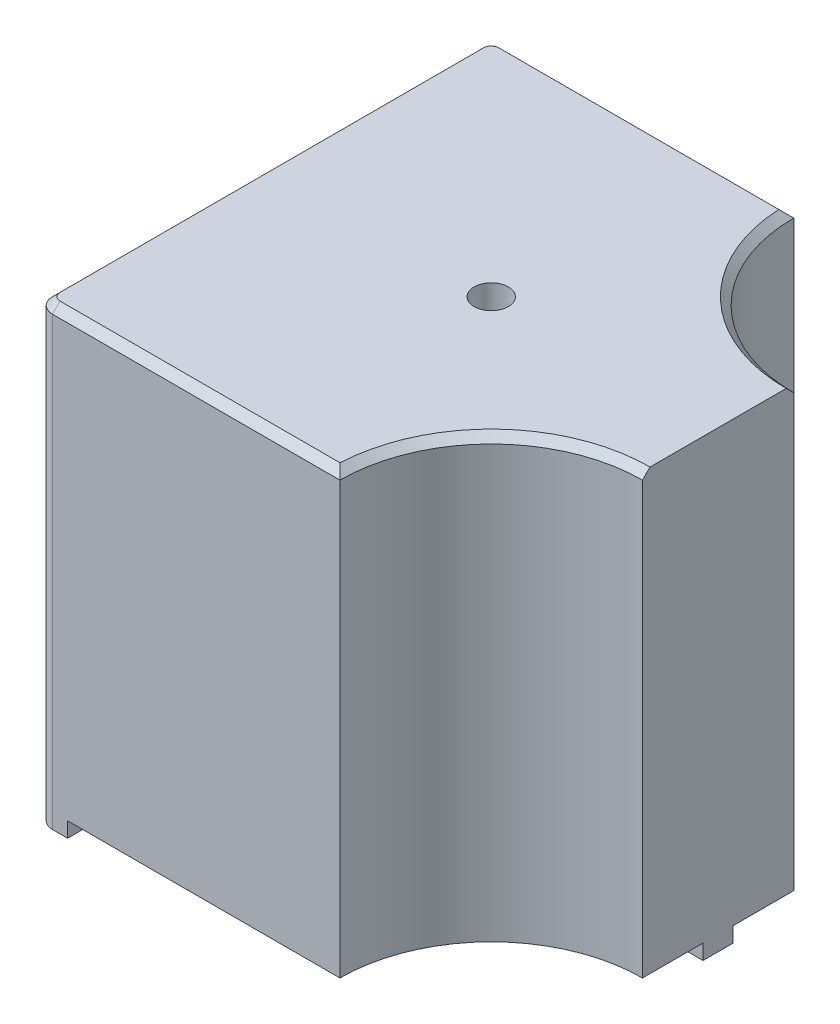
SolidWorks part; units mm, degrees
material "Copper"
ref_plane "Front" through (0, 0, 0) normal (0, 0, 1) x (1, 0, 0)
ref_plane "Top" through (0, 0, 0) normal (0, 1, 0) x (1, 0, 0)
ref_plane "Right" through (0, 0, 0) normal (1, 0, 0) x (0, 0, -1)
sketch "Sketch1" plane through (0, 0, 0) normal (0, 1, 0) x (1, 0, 0)
  line L1 (-15, 15) -> (15, 15)
  line L2 (-15, 15) -> (-15, -15)
  line L3 (-15, -15) -> (15, -15)
  line L4 (15, 15) -> (15, -15)
  line L5 (-15, 15) -> (15, -15) construction
  line L6 (-15, -15) -> (15, 15) construction
  point P0 (0, 0)
  dimension "D1" = 30
  dimension "D2" = 30
extrude "Boss-Extrude1" add sketch "Sketch1" along normal blind 30
sketch "Sketch2" plane through (0, 30, 0) normal (0, 1, 0) x (1, 0, 0)
  line L0 (15, -15) -> (15, 15) construction
  line L1 (15, 15) -> (-15, 15) construction
  arc A0 (15, 5) -> (5, 15) centre (15, 15) cw
extrude "Cut-Extrude1" cut sketch "Sketch2" against normal through all and the other way through all flip side to cut
mirror "Mirror1" about plane through (0, 0, 0) normal (0, 0, 1) of "Cut-Extrude1"
sketch "Sketch3" plane through (0, 0, 0) normal (0, -1, 0) x (1, 0, 0)
  line L0 (15, 5) -> (15, -5) construction
  line L1 (-15, 15) -> (-13, 15)
  line L2 (-15, 15) -> (-15, 13)
  line L3 (-15, 13) -> (-13, 13)
  line L4 (-13, 15) -> (-13, 13)
  line L5 (-15, -15) -> (-13, -15)
  line L6 (-15, -15) -> (-15, -13)
  line L7 (-15, -13) -> (-13, -13)
  line L8 (-13, -15) -> (-13, -13)
  line L9 (15, 1) -> (13, 1)
  line L10 (15, 1) -> (15, -1)
  line L11 (15, -1) -> (13, -1)
  line L12 (13, 1) -> (13, -1)
  dimension "D1" = 2
  dimension "D2" = 2
  dimension "D3" = 2
  dimension "D4" = 2
  dimension "D5" = 2
  dimension "D6" = 2
  dimension "D7" = 4
extrude "Cut-Extrude2" cut sketch "Sketch3" against normal blind 1 flip side to cut
hole_wizard "#8-32 Tapped Hole1" positions "Sketch5" profile "Sketch4" tap size "#8-32" standard "ANSI Inch"
sketch "Sketch5" plane through (0, 1, 0) normal (0, -1, 0) x (1, 0, 0)
  point P0 (0, 0)
sketch "Sketch4" plane through (0, 1, 0) normal (1, 0, 0) x (0, 0, -1)
  line L0 (0, 0) -> (0, 11.7566)
  line L1 (0, 11.7566) -> (1.7272, 10.7188)
  line L2 (1.7272, 10.7188) -> (1.7272, 0)
  line L5 (1.7272, 0) -> (0, 0)
  line L10 (0, 11.7566) -> (-1.7272, 10.7188) construction
  line L11 (0, -6.35) -> (0, 107.95) construction
  dimension "Tap Drill Dia." = 3.4544
  dimension "Tap Drill Depth" = 10.7188
  dimension "Drill Angle" = 118
cosmetic thread "Hole Thread3" parameters "D1"=8.3312, "D2"=4.1656
hole_wizard "#4-40 Tapped Hole1" positions "Sketch7" profile "Sketch6" tap size "#4-40" standard "ANSI Inch"
sketch "Sketch7" plane through (0, 30, 0) normal (0, 1, 0) x (-1, 0, 0)
  point P0 (0, 0)
sketch "Sketch6" plane through (0, 30, 0) normal (1, 0, 0) x (0, 0, 1)
  line L0 (0, 0) -> (0, 8.2738)
  line L1 (0, 8.2738) -> (1.1303, 7.5946)
  line L2 (1.1303, 7.5946) -> (1.1303, 0)
  line L5 (1.1303, 0) -> (0, 0)
  line L10 (0, 8.2738) -> (-1.1303, 7.5946) construction
  line L11 (0, -6.35) -> (0, 107.95) construction
  dimension "Tap Drill Dia." = 2.2606
  dimension "Tap Drill Depth" = 7.5946
  dimension "Drill Angle" = 118
cosmetic thread "Hole Thread4" parameters "D1"=5.6896, "D2"=2.8448
fillet "Fillet1" radius 1 2 edges at (-15, 15, 15) (-15, 15, -15)
chamfer "Chamfer1" distance 0.5 angle 45 8 edges at (-4.5, 30, -15) (-14.7071, 30, -14.7071) (-15, 30, 0) (-14.7071, 30, 14.7071) (7.9289, 30, -7.9289) (15, 30, 0) (7.9289, 30, 7.9289) (-4.5, 30, 15)
